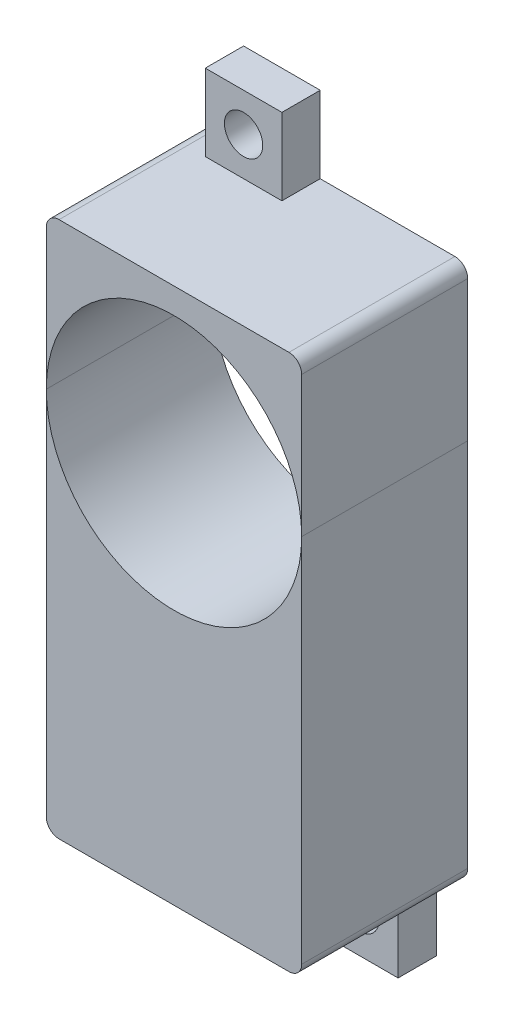
SolidWorks part; units mm, degrees
ref_plane "Front Plane" through (0, 0, 0) normal (0, 0, 1) x (1, 0, 0)
ref_plane "Top Plane" through (0, 0, 0) normal (0, 1, 0) x (1, 0, 0)
ref_plane "Right Plane" through (0, 0, 0) normal (1, 0, 0) x (0, 0, -1)
sketch "Sketch1" plane through (0, 0, 0) normal (0, 0, 1) x (1, 0, 0)
  line L0 (-10, 0) -> (10, 0) construction
  line L1 (-10, 0) -> (-10, 11)
  line L2 (10, 0) -> (10, 11)
  line L3 (9, 12) -> (-1.55, 12)
  line L4 (-7.55, 12) -> (-7.55, 18)
  line L5 (-7.55, 18) -> (-1.55, 18)
  line L6 (-1.55, 18) -> (-1.55, 12)
  line L7 (-7.55, 12) -> (-9, 12)
  line L8 (-7.55, 12) -> (-7.55, 11)
  line L9 (-7.55, 11) -> (-1.55, 11)
  line L10 (-1.55, 11) -> (-1.55, 12)
  line L11 (-10, 0) -> (-10, -29)
  line L12 (-9, -30) -> (1.55, -30)
  line L13 (10, -29) -> (10, 0)
  line L14 (7.55, -30) -> (7.55, -36.1571)
  line L15 (7.55, -36.1571) -> (1.55, -36.1571)
  line L16 (1.55, -36.1571) -> (1.55, -30)
  line L17 (7.55, -30) -> (9, -30)
  line L18 (1.55, -30) -> (1.55, -29)
  line L19 (1.55, -29) -> (7.55, -29)
  line L20 (7.55, -29) -> (7.55, -30)
  circle A1 centre (-4.55, 15) radius 1.5
  arc A2 (-9, 12) -> (-10, 11) centre (-9, 11) ccw
  arc A3 (10, 11) -> (9, 12) centre (9, 11) ccw
  circle A4 centre (0, 0) radius 10
  circle A5 centre (4.55, -33) radius 1.5
  arc A6 (-10, -29) -> (-9, -30) centre (-9, -29) ccw
  arc A7 (9, -30) -> (10, -29) centre (9, -29) ccw
  dimension "D6" = 3
  dimension "D10" = 2
  dimension "D11" = 2
  dimension "D16" = 3
  dimension "D8" = 3
  dimension "D17" = 2
  dimension "D20" = 2
  dimension "D21" = 20
  dimension "D2" = 12
  dimension "D3" = 2.45
  dimension "D4" = 6
  dimension "D5" = 6
  dimension "D7" = 1
  dimension "D9" = 3
  dimension "D12" = 30
  dimension "D13" = 2.45
  dimension "D14" = 6
  dimension "D15" = 1
  dimension "D18" = 3
  dimension "D19" = 3
  dimension "D22" = 20
extrude "Boss-Extrude2" add sketch "Sketch1" along normal mid plane 13 contours A4 L11 L12 L18 L19 L20 L17 L13 | A4 L2 A3 L3 L10 L9 L8 L7 A2 L1 | L9 L10 L6 L5 L4 L8 A1 | L20 L19 L18 L16 L15 L14 A5
sketch "Sketch3" plane through (0, 0, 6.5) normal (0, 0, 1) x (1, 0, 0)
  line L0 (-7.55, 12) -> (-1.55, 12)
  line L1 (-1.55, 12) -> (-1.55, 18)
  line L2 (-1.55, 18) -> (-7.55, 18)
  line L3 (-7.55, 18) -> (-7.55, 12)
extrude "Cut-Extrude1" cut sketch "Sketch3" against normal blind 10
sketch "Sketch4" plane through (0, 0, 6.5) normal (0, 0, 1) x (1, 0, 0)
  line L0 (1.55, -30) -> (1.55, -36.1571)
  line L1 (1.55, -36.1571) -> (7.55, -36.1571)
  line L2 (7.55, -36.1571) -> (7.55, -30)
  line L3 (7.55, -30) -> (1.55, -30)
extrude "Cut-Extrude2" cut sketch "Sketch4" against normal blind 10
